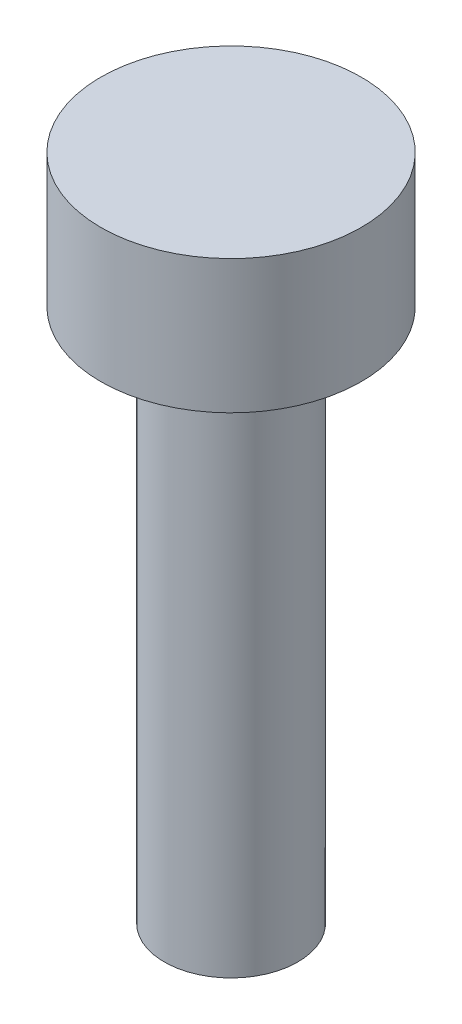
SolidWorks part; units mm, degrees
ref_plane "Front Plane" through (0, 0, 0) normal (0, 0, 1) x (1, 0, 0)
ref_plane "Top Plane" through (0, 0, 0) normal (0, 1, 0) x (1, 0, 0)
ref_plane "Right Plane" through (0, 0, 0) normal (1, 0, 0) x (0, 0, -1)
sketch "Sketch1" plane through (0, 0, 0) normal (0, 1, 0) x (1, 0, 0)
  circle A0 centre (0, 0) radius 1.95
  dimension "D1" = 3.9
extrude "Boss-Extrude1" add sketch "Sketch1" along normal blind 2
sketch "Sketch2" plane through (0, 0, 0) normal (0, -1, 0) x (1, 0, 0)
  circle A0 centre (0, 0) radius 1
  dimension "D1" = 2
extrude "Boss-Extrude2" add sketch "Sketch2" along normal blind 8
